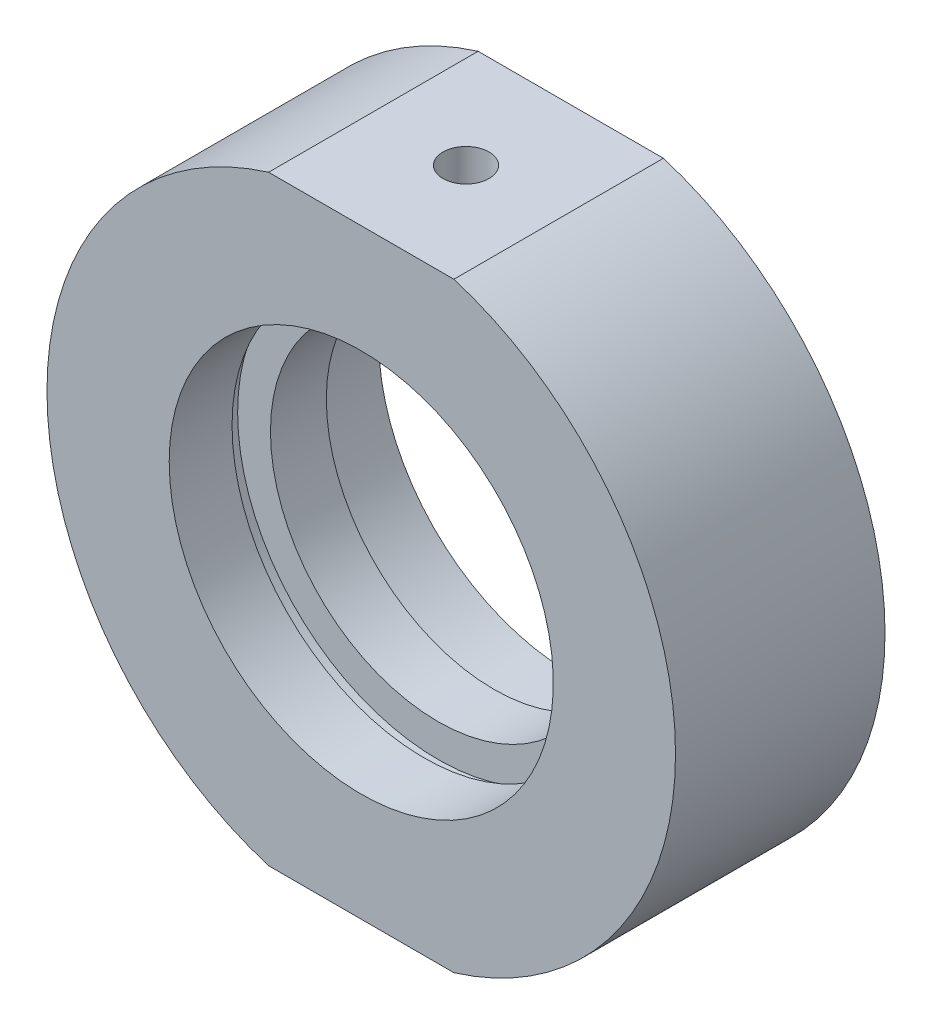
SolidWorks part; units mm, degrees
ref_plane "前视基准面" through (0, 0, 0) normal (0, 0, 1) x (1, 0, 0)
ref_plane "上视基准面" through (0, 0, 0) normal (0, 1, 0) x (1, 0, 0)
ref_plane "右视基准面" through (0, 0, 0) normal (1, 0, 0) x (0, 0, -1)
sketch "草图1" plane through (0, 0, 0) normal (0, 1, 0) x (1, 0, 0)
  line L0 (0, 31.9391) -> (0, -26.491) construction
  line L1 (22.5, 7.5) -> (22.5, -7.5)
  line L3 (14.35, 2) -> (14.35, 3)
  line L4 (14.35, 3) -> (13.75, 3)
  line L6 (22.5, -7.5) -> (13.75, -7.5)
  line L7 (13.75, -7.5) -> (13.75, -3)
  line L8 (14.35, -2) -> (12, -2)
  line L9 (12, -2) -> (12, 2)
  line L10 (12, 2) -> (14.35, 2)
  line L11 (13.75, 3) -> (13.75, 7.5)
  line L12 (13.75, 7.5) -> (22.5, 7.5)
  line L13 (14.35, -2) -> (14.35, -3)
  line L14 (14.35, -3) -> (13.75, -3)
  line L17 (35.331, 0) -> (-5.0345, 0) construction
  point P6 (12, 0)
  dimension "D2" = 12
  dimension "D3" = 13.75
  dimension "D4" = 13.75
  dimension "D5" = 15
  dimension "D6" = 5.5
  dimension "D7" = 5.5
  dimension "D8" = 14.35
  dimension "D9" = 22.5
  dimension "D10" = 14.35
  dimension "D11" = 1
  dimension "D12" = 1
  dimension "D13" = 7.5
  dimension "D18" = 0
revolve "旋转1" add sketch "草图1" angle 360 about L0
cosmetic thread "装饰螺纹线1" parameters "D2"=28.5
cosmetic thread "装饰螺纹线2" parameters "D2"=28.5
sketch "草图2" plane through (0, 0, 7.5) normal (0, 0, 1) x (1, 0, 0)
  line L0 (0, 0) -> (43.1523, 0) construction
  line L1 (-33.152, 30.7489) -> (30.8698, 30.7489)
  line L2 (-33.152, 30.7489) -> (-33.152, 21.5)
  line L3 (-33.152, 21.5) -> (30.8698, 21.5)
  line L4 (30.8698, 30.7489) -> (30.8698, 21.5)
  line L5 (30.8698, -30.7489) -> (30.8698, -21.5)
  line L6 (-33.152, -21.5) -> (30.8698, -21.5)
  line L7 (-33.152, -30.7489) -> (-33.152, -21.5)
  line L8 (-33.152, -30.7489) -> (30.8698, -30.7489)
  dimension "D1" = 21.5
extrude "切除-拉伸1" cut sketch "草图2" against normal blind 49
sketch "草图10" plane through (0, 0, 0) normal (0, 0, 1) x (1, 0, 0)
  line L0 (0, 21.5) -> (0, -21.5)
  line L1 (-6.6332, 21.5) -> (6.6332, 21.5) construction
  line L2 (-6.6332, -21.5) -> (6.6332, -21.5) construction
  line L3 (0, 0) -> (-19.4856, 11.25)
  line L4 (0, 0) -> (19.4856, 11.25)
  arc A2 (6.6332, -21.5) -> (6.6332, 21.5) centre (0, 0) ccw construction
  arc A3 (-6.6332, 21.5) -> (-6.6332, -21.5) centre (0, 0) ccw construction
  arc A4 (19.4856, 11.25) -> (6.6332, 21.5) centre (0, 0) ccw
  arc A5 (-6.6332, 21.5) -> (-19.4856, 11.25) centre (0, 0) ccw
  dimension "D1" = 60
  dimension "D2" = 60
hole_wizard "M4 螺纹孔2" positions "草图15" profile "草图16" tap size "M4" standard "ISO"
sketch "草图15" plane through (0, 21.5, 0) normal (0, 1, 0) x (1, 0, 0)
  point P0 (0, 0)
sketch "草图16" plane through (0, 21.5, 0) normal (1, 0, 0) x (0, 0, 1)
  line L0 (0, 0) -> (0, 6.4914)
  line L1 (0, 6.4914) -> (1.65, 5.5)
  line L2 (1.65, 5.5) -> (1.65, 0)
  line L5 (1.65, 0) -> (0, 0)
  line L10 (0, 6.4914) -> (-1.65, 5.5) construction
  line L11 (0, -6.35) -> (0, 107.95) construction
  dimension "螺纹孔钻头直径" = 3.3
  dimension "螺纹孔钻头深度" = 5.5
  dimension "导头角度" = 118
cosmetic thread "孔螺蚊线6"
hole_wizard "M6 螺纹孔2" positions "草图17" profile "草图18" tap size "M6" standard "ISO"
sketch "草图17" plane through (0, -21.5, 0) normal (0, -1, 0) x (-1, 0, 0)
  point P0 (0, 0)
sketch "草图18" plane through (0, -21.5, 0) normal (1, 0, 0) x (0, 0, -1)
  line L0 (0, 0) -> (0, 7.0022)
  line L1 (0, 7.0022) -> (2.5, 5.5)
  line L2 (2.5, 5.5) -> (2.5, 0)
  line L5 (2.5, 0) -> (0, 0)
  line L10 (0, 7.0022) -> (-2.5, 5.5) construction
  line L11 (0, -6.35) -> (0, 107.95) construction
  dimension "螺纹孔钻头直径" = 5
  dimension "螺纹孔钻头深度" = 5.5
  dimension "导头角度" = 118
cosmetic thread "孔螺蚊线7" parameters "D1"=5.5, "D2"=6
